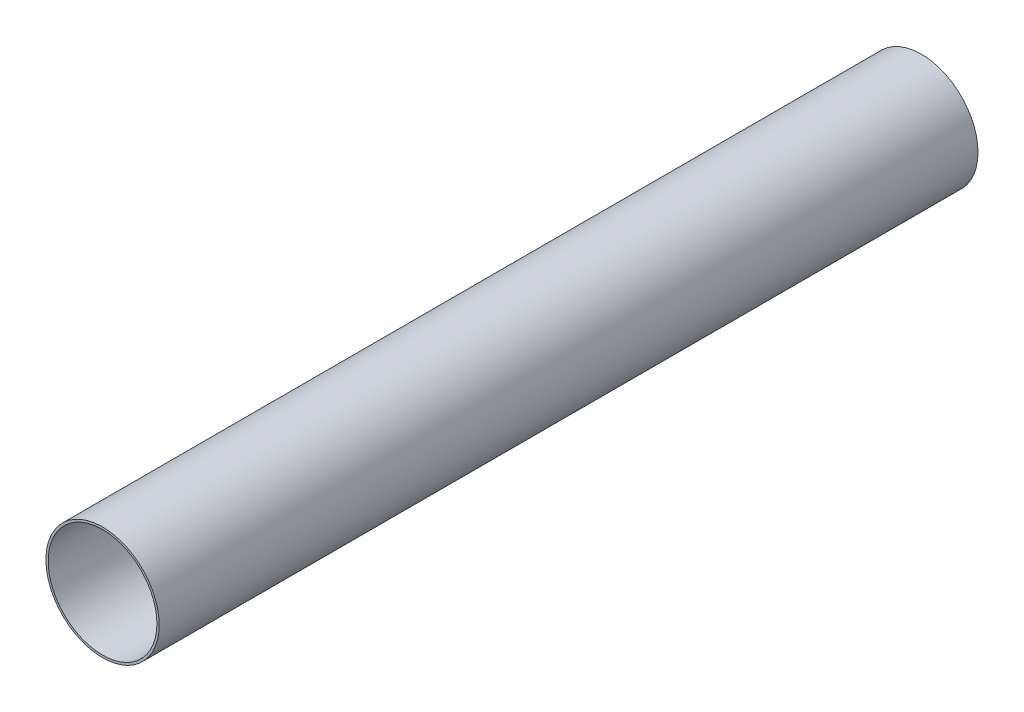
SolidWorks part; units mm, degrees
material "PVC Rigid"
ref_plane "Front Plane" through (0, 0, 0) normal (0, 0, 1) x (1, 0, 0)
ref_plane "Top Plane" through (0, 0, 0) normal (0, 1, 0) x (1, 0, 0)
ref_plane "Right Plane" through (0, 0, 0) normal (1, 0, 0) x (0, 0, -1)
sketch "Sketch1" plane through (0, 0, 0) normal (0, 0, 1) x (1, 0, 0)
  circle A0 centre (0, 0) radius 53
  circle A1 centre (0, 0) radius 55.2
  dimension "D1" = 110.4
  dimension "D2" = 106
extrude "Boss-Extrude1" add sketch "Sketch1" along normal blind 798
